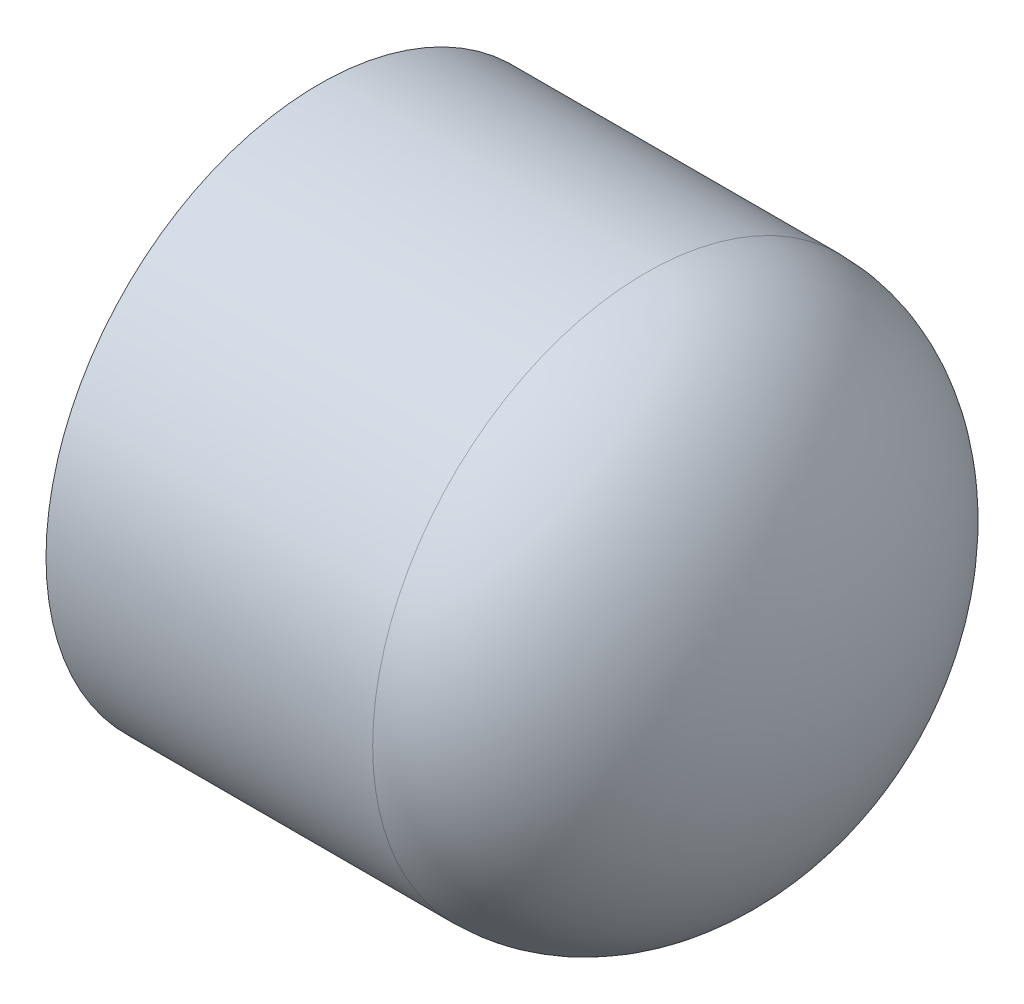
SolidWorks part; units mm, degrees
material "PVC Rigid"
ref_plane "Front Plane" through (0, 0, 0) normal (0, 0, 1) x (1, 0, 0)
ref_plane "Top Plane" through (0, 0, 0) normal (0, 1, 0) x (1, 0, 0)
ref_plane "Right Plane" through (0, 0, 0) normal (1, 0, 0) x (0, 0, -1)
sketch "Sketch0" plane through (0, 0, 0) normal (0, 0, 1) x (1, 0, 0)
  line L3 (-16.0401, 0) -> (16.0401, 0) construction
  line L4 (-16.0401, 16.9926) -> (-16.0401, -16.9926) construction
  line L5 (4.2799, 13.2842) -> (-16.0401, 13.4366) construction
  line L6 (4.2799, 13.2842) -> (4.2799, -13.2842) construction
  line L7 (4.2799, -13.2842) -> (-16.0401, -13.4366) construction
  line L8 (-16.0401, 13.4366) -> (-16.0401, -13.4366) construction
  line L14 (4.2799, 10.4648) -> (4.2799, -10.4648) construction
  point P0 (4.2799, 0)
  dimension "H" = 11.7602
  dimension "M" = 33.9852
  dimension "OD A" = 26.8732
  dimension "OD B" = 26.5684
  dimension "ID" = 20.9296
  dimension "L" = 32.0802
  dimension "C" = 20.32
sketch "Sketch1" plane through (0, 0, 0) normal (0, 0, 1) x (1, 0, 0)
  line L1 (-16.0401, 0) -> (16.0401, 0) construction
  line L2 (-16.0401, 0) -> (16.0401, 0) construction
  line L3 (12.3317, 0) -> (16.0401, 0)
  line L4 (-16.0401, -16.9926) -> (-16.0401, -13.4366)
  line L5 (-16.0401, -13.4366) -> (4.2799, -13.2842)
  line L6 (4.2799, -13.2842) -> (4.2799, -16.9926) construction
  line L9 (4.2799, -16.9926) -> (-16.0401, -16.9926)
  ellipse E2 centre (4.2799, 0) end of major axis (4.2799, 16.9926) minor radius 11.7602 (4.2799, -16.9926) -> (16.0401, 0) ccw
  ellipse E3 centre (4.2799, 0) end of major axis (4.2799, -13.2842) minor radius 8.0518 (4.2799, -13.2842) -> (12.3317, 0) ccw
revolve "Revolve1" add sketch "Sketch1" angle 360 about L1
